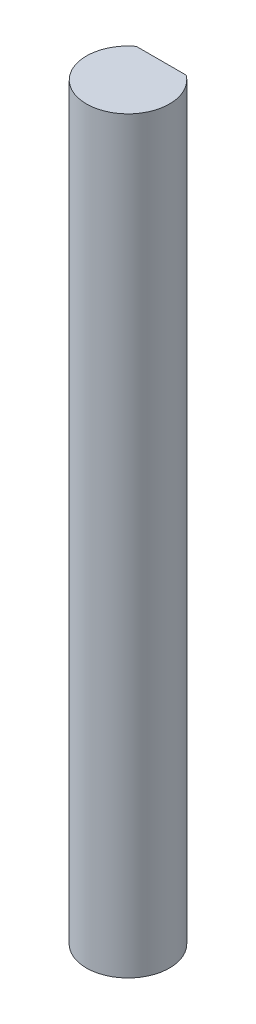
SolidWorks part; units mm, degrees
ref_plane "Front Plane" through (0, 0, 0) normal (0, 0, 1) x (1, 0, 0)
ref_plane "Top Plane" through (0, 0, 0) normal (0, 1, 0) x (1, 0, 0)
ref_plane "Right Plane" through (0, 0, 0) normal (1, 0, 0) x (0, 0, -1)
sketch "Sketch1" plane through (0, 0, 0) normal (0, 1, 0) x (1, 0, 0)
  line L0 (-1.905, 2.54) -> (1.905, 2.54)
  arc A0 (-1.905, 2.54) -> (1.905, 2.54) centre (0, 0) ccw
  dimension "D1" = 6.35
  dimension "D2" = 2.54
extrude "Boss-Extrude1" add sketch "Sketch1" along normal blind 57.15
